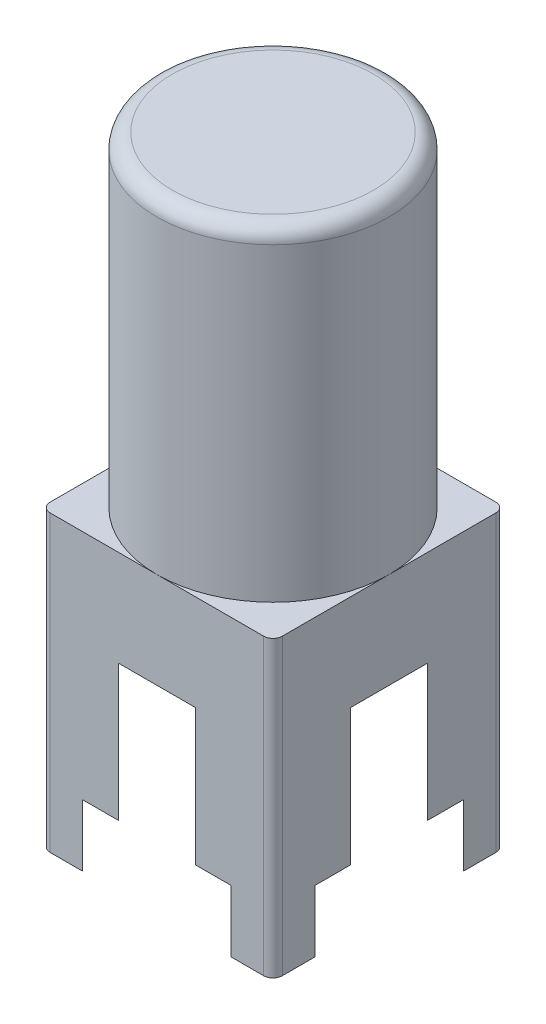
SolidWorks part; units mm, degrees
ref_plane "Front Plane" through (0, 0, 0) normal (0, 0, 1) x (1, 0, 0)
ref_plane "Top Plane" through (0, 0, 0) normal (0, 1, 0) x (1, 0, 0)
ref_plane "Right Plane" through (0, 0, 0) normal (1, 0, 0) x (0, 0, -1)
sketch "Sketch1" plane through (0, 0, 0) normal (0, 1, 0) x (1, 0, 0)
  line L1 (-4.7625, 4.7625) -> (4.7625, 4.7625)
  line L2 (-4.7625, 4.7625) -> (-4.7625, -4.7625)
  line L3 (-4.7625, -4.7625) -> (4.7625, -4.7625)
  line L4 (4.7625, 4.7625) -> (4.7625, -4.7625)
  line L5 (-4.7625, 4.7625) -> (4.7625, -4.7625) construction
  line L6 (-4.7625, -4.7625) -> (4.7625, 4.7625) construction
  point P0 (0, 0)
  dimension "D1" = 9.525
  dimension "D2" = 9.525
extrude "Boss-Extrude1" add sketch "Sketch1" against normal blind 12.065
sketch "Sketch2" plane through (0, 0, 0) normal (0, 1, 0) x (1, 0, 0)
  circle A0 centre (0, 0) radius 4.7625
extrude "Boss-Extrude2" add sketch "Sketch2" along normal blind 13.335
fillet "Fillet1" radius 0.635 1 edges at (0, 13.335, 4.7625)
sketch "Sketch3" plane through (0, -12.065, 0) normal (0, -1, 0) x (1, 0, 0)
  circle A0 centre (0, 0) radius 5.6515
extrude "Cut-Extrude1" cut sketch "Sketch3" against normal blind 2.54
sketch "Sketch4" plane through (0, -9.525, 0) normal (0, -1, 0) x (1, 0, 0)
  circle A0 centre (0, 0) radius 5.0165
extrude "Cut-Extrude2" cut sketch "Sketch4" against normal blind 5.588
sketch "Sketch5" plane through (0, -3.937, 0) normal (0, -1, 0) x (1, 0, 0)
  circle A1 centre (0, 0) radius 3.81
  dimension "D1" = 7.62
extrude "Boss-Extrude3" add sketch "Sketch5" along normal blind 1.27
fillet "Fillet2" radius 0.635 1 edges at (0, -5.207, -3.81)
sketch "Sketch6" plane through (0, -3.937, 0) normal (0, -1, 0) x (1, 0, 0)
  circle A0 centre (0, 0) radius 0.889
  dimension "D1" = 1.778
extrude "Boss-Extrude4" add sketch "Sketch6" along normal up to surface (8.128 mm away) up to face at (-4.2204, -12.065, 4.2204)
fillet "Fillet4" radius 0.381 4 edges at (-4.7625, -6.0325, -4.7625) (4.7625, -6.0325, -4.7625) (4.7625, -6.0325, 4.7625) (-4.7625, -6.0325, 4.7625)
